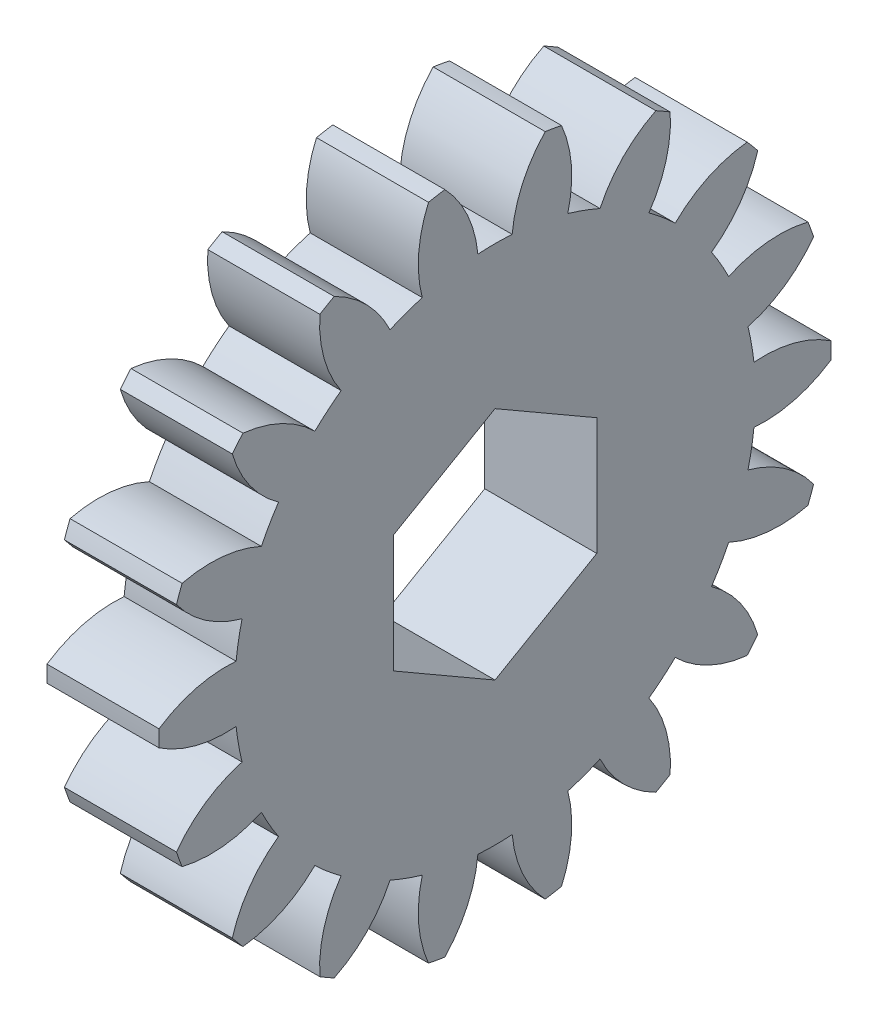
SolidWorks part; units mm, degrees
ref_plane "Plane1" through (0, 0, 0) normal (0, 0, 1) x (1, 0, 0)
ref_plane "Plane2" through (0, 0, 0) normal (0, 1, 0) x (1, 0, 0)
ref_plane "Plane3" through (0, 0, 0) normal (1, 0, 0) x (0, 0, -1)
sketch "HoldingSke" plane through (0, 0, 0) normal (0, 1, 0) x (1, 0, 0)
  line L0 (0, 0) -> (1.0567, -0.3434)
  line L1 (-15, 0) -> (100, 0) construction
  line L2 (0, 0) -> (-2.1039, 2.3779)
  line L3 (0, 0) -> (-11.863, 4.5341)
  line L4 (0, 0) -> (8.2133, 2.6687)
  line L5 (0, 0) -> (-46.8476, -17.4728)
  line L6 (0, 0) -> (-2.4869, -1.6779)
  line L7 (-2.1039, 2.3779) -> (8.6587, 51.2062)
  line L8 (-76.2, 54.61) -> (-75.2, 54.61)
  line L9 (-71.009, 38.7566) -> (-53.1078, 45.2721)
  line L10 (-76.2, 71.12) -> (104.1128, 71.12)
  line L11 (0, 0) -> (-3, 0)
  line L12 (-76.2, 101.6) -> (-76.166, 101.6)
  line L13 (24.9733, 27.94) -> (52.9518, 28.4284)
  line L14 (24.9733, 27.94) -> (24.9743, 27.94)
  line L15 (24.9733, 27.94) -> (100.4006, 29.5858)
  line L16 (-63.627, -0.9) -> (-12.827, -0.9)
  circle A0 centre (0, 0) radius 3
  circle A1 centre (0, 0) radius 6.974
  circle A2 centre (0, 0) radius 37.5
  circle A3 centre (0, 0) radius 3
  dimension "MHD" = 13.948
  dimension "Hub_dia" = 75
  dimension "Bore" = 6
  dimension "MBD" = 6
  dimension "Num_teeth" = 18
  dimension "Pitch" = 1.1111
  dimension "Overall_len" = 50
  dimension "Show_teeth" = 18
  dimension "Thickness" = 3
  dimension "OAL" = 50.0004
  dimension "T_dim" = 1
  dimension "Ap" = 20
  dimension "H" = 19.05
  dimension "Pitch_radius" = 180.3128
  dimension "Width" = 3
  dimension "Backlash" = 0.034
  dimension "Addendum_fac" = 1
  dimension "Dedendum_fac" = 1.25
  dimension "Clearance_fac" = 0.25
  dimension "Dedendum_add" = 0.001
  dimension "Module" = 0.9
sketch "BasProSke" plane through (0, 0, 0) normal (0, 1, 0) x (1, 0, 0)
  line L0 (-10, 0) -> (60, 0) construction
  line L1 (0, 0) -> (0, 9)
  line L2 (0, 0) -> (3, 0)
  line L3 (3, 0) -> (3, 9)
  line L4 (3, 9) -> (0, 9)
  dimension "Thickness" = 3
  dimension "Diameter" = 18
revolve "Base-Revolve" add sketch "BasProSke" angle 360 about L0
sketch "TooCutSke" plane through (0, 0, 0) normal (1, 0, 0) x (0, 0, -1)
  line L1 (0, 0) -> (0, 107) construction
  line L2 (0, 0) -> (-0.7654, 8.0638) construction
  line L3 (0, 0) -> (-2.8041, 15.903) construction
  line L4 (-0.7654, 8.0638) -> (-1.4021, 7.9515) construction
  arc A0 (0.4593, 6.9589) -> (-0.4593, 6.9589) centre (0, 0) ccw
  arc A1 (1.3655, 8.9215) -> (-1.3655, 8.9215) centre (0, 0) ccw
  circle A2 centre (0, 0) radius 8.1 construction
  circle A3 centre (0, 0) radius 7.6115 construction
  arc A4 (-0.4593, 6.9589) -> (-1.3655, 8.9215) centre (-3.6854, 6.6598) ccw
  arc A5 (1.3655, 8.9215) -> (0.4593, 6.9589) centre (3.6854, 6.6598) ccw
  dimension "Root_dia" = 13.948
  dimension "Overcut_dia" = 18.0508
  dimension "Pitch_dia" = 16.2
  dimension "Base_dia" = 15.223
  dimension "Flank_rad" = 3.24
  dimension "Half_ang" = 10
  dimension "Half_CT" = 0.6465
extrude "ToothCut" cut sketch "TooCutSke" along normal through all
fillet "Breaks" [suppressed] radius 0.018
fillet "RootFillets" [suppressed] radius 0.226
pattern_circular "TeethCuts" count 18 every 20 about axis through (-10, 0, 0) along (1, 0, 0) of "ToothCut", "RootFillets", "Breaks"
sketch "HubNeaOneSke" plane through (0, 0, 0) normal (-1, 0, 0) x (0, 0, 1)
  circle A0 centre (0, 0) radius 6.974
  dimension "Diameter" = 13.948
extrude "HubNearOne" [suppressed] add sketch "HubNeaOneSke" along normal blind 47.0004
sketch "HubNeaBotSke" plane through (0, 0, 0) normal (-1, 0, 0) x (0, 0, 1)
  circle A0 centre (0, 0) radius 6.974
  dimension "Diameter" = 13.948
extrude "HubNearBoth" [suppressed] add sketch "HubNeaBotSke" along normal blind 23.5002
ref_plane "FarPln" through (3, 0, 0) normal (1, 0, 0) x (0, 0, -1)
sketch "HubFarSke" plane through (3, 0, 0) normal (1, 0, 0) x (0, 0, -1)
  circle A0 centre (0, 0) radius 6.974
  dimension "Diameter" = 13.948
extrude "HubFar" [suppressed] add sketch "HubFarSke" along normal blind 23.5002
sketch "KeySke" plane through (0, 0, 0) normal (1, 0, 0) x (0, 0, -1)
  line L0 (-1, 0) -> (-1, 4)
  line L1 (-1, 4) -> (1, 4)
  line L2 (1, 4) -> (1, 0)
  line L3 (0, 0) -> (0, 34) construction
  line L4 (-1, 0) -> (1, 0)
  dimension "Offset" = 4
  dimension "Width" = 2
extrude "Keyway" [suppressed] cut sketch "KeySke" along normal mid plane 100.0007
pattern_circular "Keyway2" [suppressed] count 2 every 90 about axis through (-10, 0, 0) along (1, 0, 0)
sketch "Sketch1" plane through (3, 0, 0) normal (1, 0, 0) x (0, 0, -1)
  line L1 (0, 3.1466) -> (-2.725, 1.5733)
  line L2 (-2.725, 1.5733) -> (-2.725, -1.5733)
  line L3 (-2.725, -1.5733) -> (0, -3.1466)
  line L4 (0, -3.1466) -> (2.725, -1.5733)
  line L5 (2.725, -1.5733) -> (2.725, 1.5733)
  line L6 (2.725, 1.5733) -> (0, 3.1466)
  circle A1 centre (0, 0) radius 2.725 construction
  dimension "D1" = 5.45
extrude "Cut-Extrude1" cut sketch "Sketch1" against normal through all
equation "' \"Module@HoldingSke\" = 6.35"
equation "' \"Num_teeth@HoldingSke\" = 12"
equation "' \"Ap@HoldingSke\" =  20"
equation "' \"Ap@HoldingSke\" = 20"
equation "' \"Width@HoldingSke\" = 0.5 * 25.4"
equation "' \"Hub_dia@HoldingSke\"= 1 * 25.4"
equation "' \"Hub_dia@HoldingSke\" = 1 * 25.4"
equation "' \"Overall_len@HoldingSke\" = 1.0 * 25.4"
equation "' \"Bore@HoldingSke\" = 0.75 * 25.4"
equation "' \"T_dim@HoldingSke\" = 0.1 * 25.4"
equation "' \"Width@KeySke\" = 0.25 * 25.4"
equation "' \"Show_teeth@HoldingSke\" = 13"
equation "' \"Backlash@HoldingSke\" = 0.009 * 25.4"
equation "' \"Addendum_fac@HoldingSke\" = 1.0"
equation "' \"Dedendum_fac@HoldingSke\" = 1.25"
equation "' \"Dedendum_add@HoldingSke\" = 0.00005 * 25.4"
equation "' \"Clearance_fac@HoldingSke\" = 0.25"
equation "\"Pitch@HoldingSke\" = 1 / \"Module@HoldingSke\""
equation "\"Overcut_dia@TooCutSke\" = (\"Num_teeth@HoldingSke\" + 2 * \"Addendum_fac@HoldingSke\") / \"Pitch@HoldingSke\" + 0.002 * 25.4"
equation "\"Pitch_dia@TooCutSke\" = \"Num_teeth@HoldingSke\" / \"Pitch@HoldingSke\""
equation "\"Base_dia@TooCutSke\" = \"Num_teeth@HoldingSke\" / \"Pitch@HoldingSke\" * cos((\"Ap@HoldingSke\"  * 3.14159265 / 180))"
equation "\"Root_dia@TooCutSke\" = (\"Num_teeth@HoldingSke\" + 2) / \"Pitch@HoldingSke\" - 2 * (\"Addendum_fac@HoldingSke\" + \"Dedendum_fac@HoldingSke\") / \"Pitch@HoldingSke\" - \"Dedendum_add@HoldingSke\" * 2"
equation "\"Half_ang@TooCutSke\" = 180 / \"Num_teeth@HoldingSke\""
equation "\"Half_CT@TooCutSke\" = \"Num_teeth@HoldingSke\" / \"Pitch@HoldingSke\" * sin((3.14159265 / 2 / \"Num_teeth@HoldingSke\")) / 2 - 7 * \"Backlash@HoldingSke\" / 4"
equation "\"Flank_rad@TooCutSke\" = \"Num_teeth@HoldingSke\" / \"Pitch@HoldingSke\" / 5"
equation "\"Radius@RootFillets\" = \"Clearance_fac@HoldingSke\" / \"Pitch@HoldingSke\" + \"Dedendum_add@HoldingSke\""
equation "\"Break_rad@Breaks\" = 0.02 / \"Pitch@HoldingSke\""
equation "\"Thickness@HoldingSke\" = \"Width@HoldingSke\""
equation "\"OAL@HoldingSke\" = \"Thickness@HoldingSke\""
equation "\"MHD@HoldingSke\" = (\"Num_teeth@HoldingSke\" + 2) / \"Pitch@HoldingSke\" - 2 * (\"Addendum_fac@HoldingSke\" + \"Dedendum_fac@HoldingSke\")  / \"Pitch@HoldingSke\" - \"Dedendum_add@HoldingSke\" * 2"
equation "\"MBD@HoldingSke\" = (\"Num_teeth@HoldingSke\" + 2) / \"Pitch@HoldingSke\" - 2 * (\"Addendum_fac@HoldingSke\" + \"Dedendum_fac@HoldingSke\")  / \"Pitch@HoldingSke\" - \"Dedendum_add@HoldingSke\" * 2 - 0.002 * 25.4"
equation "\"MHD@HoldingSke\" = ((sgn( \"MHD@HoldingSke\" - \"Hub_dia@HoldingSke\" )-1)*( \"MHD@HoldingSke\" - \"Hub_dia@HoldingSke\" ))/-2+ \"Hub_dia@HoldingSke\""
equation "\"MBD@HoldingSke\" = ((sgn( \"MBD@HoldingSke\" - \"Bore@HoldingSke\" )-1)*( \"MBD@HoldingSke\" - \"Bore@HoldingSke\" ))/-2+ \"Bore@HoldingSke\""
equation "\"OAL@HoldingSke\" = ((sgn( \"OAL@HoldingSke\" - \"Overall_len@HoldingSke\" )+1)*( \"OAL@HoldingSke\" - \"Overall_len@HoldingSke\" ))/2 + \"Overall_len@HoldingSke\" + 0.000002 * 25.4"
equation "\"Num_teeth@TeethCuts\" = int( \"Show_teeth@HoldingSke\" ) + 1"
equation "\"Num_teeth@TeethCuts\" = ((sgn( \"Num_teeth@TeethCuts\" - \"Num_teeth@HoldingSke\" )-1)*( \"Num_teeth@TeethCuts\" - \"Num_teeth@HoldingSke\" ))/-2+ \"Num_teeth@HoldingSke\""
equation "\"Num_teeth@TeethCuts\" = ((sgn( \"Num_teeth@TeethCuts\" - 2.0)+1)*( \"Num_teeth@TeethCuts\" - 2.0))/2 +2.0"
equation "\"Angle@TeethCuts\" = 360.0 / \"Num_teeth@HoldingSke\""
equation "\"Diameter@BasProSke\" = (\"Num_teeth@HoldingSke\" + 2 * \"Addendum_fac@HoldingSke\") / \"Pitch@HoldingSke\""
equation "\"Thickness@BasProSke\"  = \"Thickness@HoldingSke\""
equation "' \"Fillet_rad@BasProSke\" =  \"Thickness@HoldingSke\" * 0.05"
equation "' \"Fillet_rad@BasProSke\" = \"Thickness@HoldingSke\" * 0.05"
equation "\"MHD@HoldingSke\" = ((sgn( \"MHD@HoldingSke\" - \"Root_dia@TooCutSke\" )-1)*( \"MHD@HoldingSke\" - \"Root_dia@TooCutSke\" ))/-2+ \"Root_dia@TooCutSke\""
equation "\"Diameter@HubNeaOneSke\" = \"MHD@HoldingSke\""
equation "\"Length@HubNearOne\" = \"OAL@HoldingSke\" - \"Thickness@BasProSke\""
equation "\"Diameter@HubNeaBotSke\" = \"MHD@HoldingSke\""
equation "\"Length@HubNearBoth\" = ( \"OAL@HoldingSke\" - \"Thickness@BasProSke\" ) / 2.0"
equation "\"Thickness@FarPln\" = \"Thickness@BasProSke\""
equation "\"Diameter@HubFarSke\" = \"MHD@HoldingSke\""
equation "\"Length@HubFar\" = ( \"OAL@HoldingSke\" - \"Thickness@BasProSke\" ) / 2.0"
equation "\"D1@Keyway\" = \"OAL@HoldingSke\" * 2.0"
equation "\"Offset@KeySke\" = \"T_dim@HoldingSke\" + \"MBD@HoldingSke\" / 2.0"
